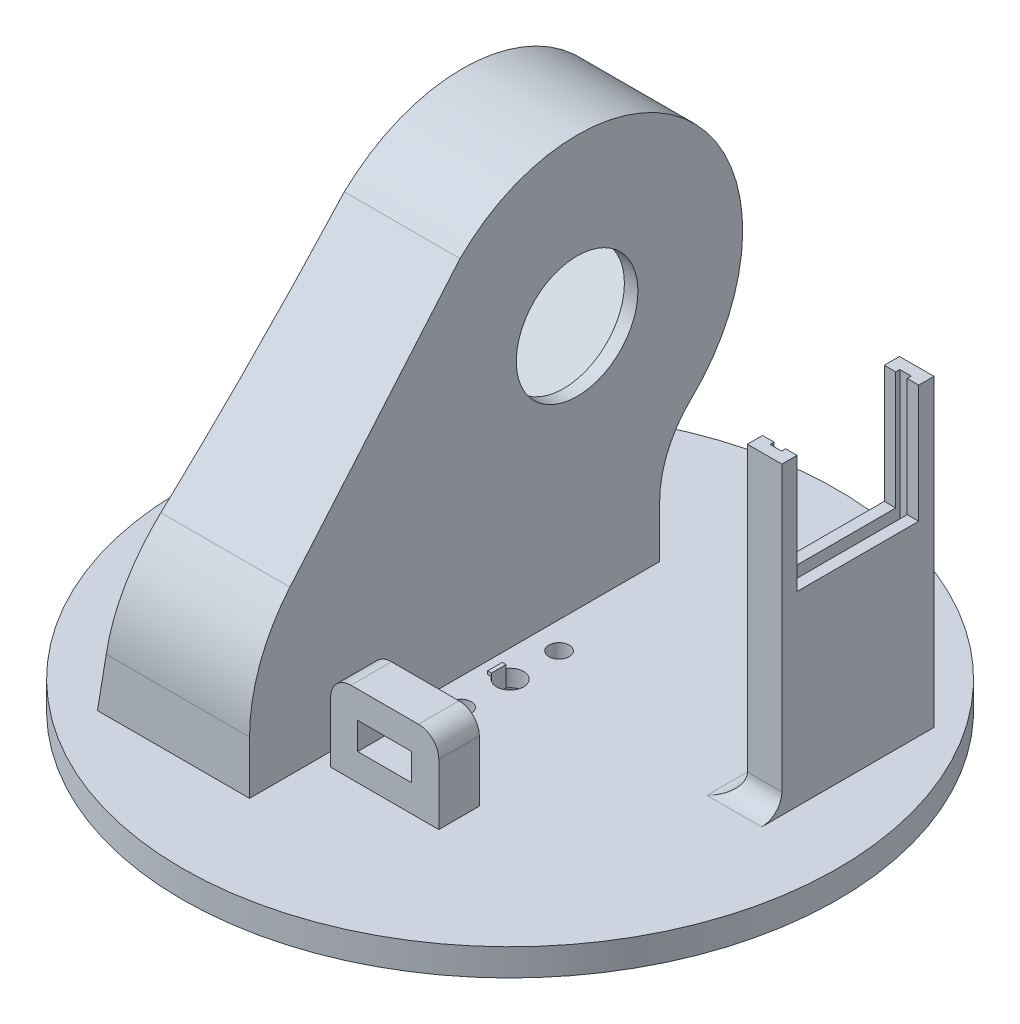
SolidWorks part; units mm, degrees
ref_plane "Front Plane" through (0, 0, 0) normal (0, 0, 1) x (1, 0, 0)
ref_plane "Top Plane" through (0, 0, 0) normal (0, 1, 0) x (1, 0, 0)
ref_plane "Right Plane" through (0, 0, 0) normal (1, 0, 0) x (0, 0, -1)
sketch "Sketch2" plane through (0, 0, 0) normal (0, 1, 0) x (1, 0, 0)
  circle A0 centre (0, 0) radius 48.5
  dimension "D1" = 97
extrude "Boss-Extrude1" add sketch "Sketch2" along normal blind 4
sketch "Sketch4" plane through (0, 0, 0) normal (0, -1, 0) x (1, 0, 0)
  circle A0 centre (0, 7.25) radius 1.5
  circle A1 centre (0, -7.25) radius 1.5
  dimension "D1" = 3
  dimension "D2" = 3
  dimension "D3" = 14.5
  dimension "D4" = 7.25
extrude "Cut-Extrude2" cut sketch "Sketch4" against normal through all
sketch "Sketch5" plane through (0, 0, 0) normal (0, -1, 0) x (1, 0, 0)
  circle A0 centre (0, 0) radius 3.75
  dimension "D1" = 7.5
extrude "Cut-Extrude3" cut sketch "Sketch5" against normal blind 1.5
ref_plane "Plane1" through (-4, 0, 0) normal (1, 0, 0) x (0, 0, -1)
sketch "Sketch7" plane through (-4, 0, 0) normal (1, 0, 0) x (0, 0, -1)
  line L0 (23.1299, 11.6445) -> (23.1299, 4)
  line L5 (48.5, 4) -> (-48.5, 4) construction
  line L6 (-27.2273, 29.5362) -> (-1.2843, 55.4793)
  line L7 (-43.5609, 4) -> (23.1299, 4)
  line L11 (-34.5496, 4) -> (-34.5496, 11.8586)
  arc A4 (28.7298, 24.692) -> (-1.2843, 55.4793) centre (13.9185, 40.2765) ccw
  arc A5 (28.7298, 24.692) -> (23.1299, 11.6445) centre (41.1299, 11.6445) ccw
  arc A6 (-27.2273, 29.5362) -> (-34.5496, 11.8586) centre (-9.5496, 11.8586) ccw
  dimension "D1" = 25
  dimension "D4" = 43
  dimension "D3" = 18
  dimension "D5" = 45
extrude "Boss-Extrude2" add sketch "Sketch7" against normal blind 14
ref_plane "Plane2" through (-6, 0, 0) normal (1, 0, 0) x (0, 0, -1)
sketch "Sketch8" plane through (-6, 0, 0) normal (1, 0, 0) x (0, 0, -1)
  line L0 (-27.2273, 29.5362) -> (-1.2843, 55.4793) construction
  line L1 (-15.2496, 25.9576) -> (13.7417, 54.9489)
  line L2 (-15.2496, 25.9576) -> (-0.4004, 11.1083)
  line L3 (-0.4004, 11.1083) -> (28.591, 40.0997)
  line L4 (13.7417, 54.9489) -> (28.591, 40.0997)
  line L5 (-15.2496, 25.9576) -> (28.591, 40.0997) construction
  line L6 (-0.4004, 11.1083) -> (13.7417, 54.9489) construction
  point P0 (6.6707, 33.0286)
  point P11 (13.9185, 40.2765)
  dimension "D1" = 41
  dimension "D2" = 21
  dimension "D3" = 90
  dimension "D4" = 20.5
  dimension "D5" = 90
  dimension "D6" = 10.25
  dimension "D7" = 10.5
extrude "Cut-Extrude5" cut sketch "Sketch8" against normal up to next
sketch "Sketch9" plane through (-18, 0, 0) normal (-1, 0, 0) x (0, 0, 1)
  line L0 (-13.7417, 54.9489) -> (-28.591, 40.0997) construction
  line L3 (-21.1664, 47.5243) -> (-22.536, 48.894) construction
  circle A0 centre (-20.1057, 53.5347) radius 1.3
  circle A1 centre (-27.1768, 46.4637) radius 1.3
  circle A2 centre (6.7644, 12.5225) radius 1.3
  circle A3 centre (13.8354, 19.5936) radius 1.3
  dimension "D1" = 2.6
  dimension "D5" = 5
  dimension "D6" = 90
  dimension "D2" = 3.5
  dimension "D3" = 2
  dimension "D4" = 2
extrude "Cut-Extrude6" cut sketch "Sketch9" against normal blind 7.5
sketch "Sketch11" plane through (-4, 0, 0) normal (1, 0, 0) x (0, 0, -1)
  circle A0 centre (13.9185, 40.2765) radius 9
  dimension "D1" = 18
extrude "Cut-Extrude9" cut sketch "Sketch11" against normal up to next
sketch "Sketch17" plane through (-18, 0, 0) normal (-1, 0, 0) x (0, 0, 1)
  line L0 (29.3486, 31.6576) -> (3.4056, 57.6006)
  line L1 (-26.1299, 11.6445) -> (-26.1299, 1)
  line L2 (-26.1299, 1) -> (37.5496, 1)
  line L3 (37.5496, 1) -> (37.5496, 11.8586)
  line L4 (27.2273, 29.5362) -> (1.2843, 55.4793)
  line L5 (-23.1299, 11.6445) -> (-23.1299, 4)
  line L6 (-23.1299, 4) -> (34.5496, 4)
  line L7 (34.5496, 4) -> (34.5496, 11.8586)
  line L9 (-23.1299, 11.6445) -> (-23.1299, 4)
  line L10 (-23.1299, 4) -> (34.5496, 4)
  line L11 (34.5496, 4) -> (34.5496, 11.8586)
  line L12 (-26.1299, 4) -> (37.5496, 4)
  line L13 (48.5, 4) -> (-48.5, 4) construction
  line L14 (3.4056, 57.6006) -> (28.5745, 28.0776)
  line L15 (1.2843, 55.4793) -> (26.295, 26.1272)
  line L16 (31.5496, 11.8586) -> (31.5496, 4)
  line L18 (27.2273, 29.5362) -> (1.2843, 55.4793) construction
  arc A0 (3.4056, 57.6006) -> (-30.7965, 22.5174) centre (-13.9185, 40.2765) ccw
  arc A1 (-26.1299, 11.6445) -> (-30.7965, 22.5174) centre (-41.1299, 11.6445) ccw
  arc A2 (37.5496, 11.8586) -> (29.3486, 31.6576) centre (9.5496, 11.8586) ccw
  arc A3 (1.2843, 55.4793) -> (-28.7298, 24.692) centre (-13.9185, 40.2765) ccw
  arc A4 (-23.1299, 11.6445) -> (-28.7298, 24.692) centre (-41.1299, 11.6445) ccw
  arc A5 (34.5496, 11.8586) -> (27.2273, 29.5362) centre (9.5496, 11.8586) ccw
  arc A6 (1.2843, 55.4793) -> (-28.7298, 24.692) centre (-13.9185, 40.2765) ccw
  arc A7 (-23.1299, 11.6445) -> (-28.7298, 24.692) centre (-41.1299, 11.6445) ccw
  arc A8 (34.5496, 11.8586) -> (27.2273, 29.5362) centre (9.5496, 11.8586) ccw
  arc A9 (31.5496, 11.8586) -> (25.106, 27.4149) centre (9.5496, 11.8586) ccw
  line M16 (27.2273, 29.5362) -> (1.2843, 55.4793)
  arc M17 (1.2843, 55.4793) -> (-28.7298, 24.692) centre (-13.9185, 40.2765) ccw
  arc M18 (-28.7298, 24.692) -> (-23.1299, 11.6445) centre (-41.1299, 11.6445) cw
  line M19 (-23.1299, 11.6445) -> (-23.1299, 4)
  line M21 (34.5496, 4) -> (34.5496, 11.8586)
  arc M22 (34.5496, 11.8586) -> (27.2273, 29.5362) centre (9.5496, 11.8586) ccw
  dimension "D1" = 0
  dimension "D2" = 3
  dimension "D3" = 3
extrude "Boss-Extrude7" add sketch "Sketch17" along normal blind 9 and the other way up to surface (14 mm away) contours A9 L16 L12 L15 M21 M22 M16 | A1 L1 L12 L14 A0 M19 M18 M17 M16 M22 other way up to face at (-4, 40.2765, -22.9185)
sketch "Sketch25" plane through (-18, 0, 0) normal (-1, 0, 0) x (0, 0, 1)
  line L0 (-23.1299, 11.6445) -> (-23.1299, 4)
  line L1 (48.5, 4) -> (-48.5, 4) construction
  line L2 (-23.1299, 11.6445) -> (-23.1299, 4) construction
  line L3 (1.2843, 55.4793) -> (26.295, 26.1272) construction
  line L4 (31.5496, 4) -> (-23.1299, 4) construction
  line L5 (31.5496, 11.8586) -> (31.5496, 4) construction
  line L6 (31.5496, 4) -> (-23.1299, 4)
  line L7 (31.5496, 11.8586) -> (31.5496, 4)
  line L8 (1.2843, 55.4793) -> (26.295, 26.1272)
  arc A0 (-23.1299, 11.6445) -> (-28.7298, 24.692) centre (-41.1299, 11.6445) ccw construction
  arc A1 (1.2843, 55.4793) -> (-28.7298, 24.692) centre (-13.9185, 40.2765) ccw construction
  arc A2 (-23.1299, 11.6445) -> (-28.7298, 24.692) centre (-41.1299, 11.6445) ccw
  arc A3 (31.5496, 11.8586) -> (26.295, 26.1272) centre (9.5496, 11.8586) ccw construction
  arc A4 (31.5496, 11.8586) -> (26.295, 26.1272) centre (9.5496, 11.8586) ccw
  spline S0 degree 3 poles (-28.7298, 24.692) (-21.9549, 18.2532) (-19.0941, 12.798) (-15.1299, 4) knots 0 0 0 0 1 1 1 1
  spline S1 degree 2 poles (11.7516, 43.195) (26.5513, 25.8264) (25.5496, 4) knots 0 0 0 1 1 1
  dimension "D2" = 8
  dimension "D1" = 6
extrude "Boss-Extrude10" add sketch "Sketch25" along normal up to surface (9 mm away) contours S0 L6 L0 A2 | A4 S1 A2 S0 L8 up to face at (-27, 22.2911, 0.3951)
sketch "Sketch26" plane through (0, 0, 0) normal (0, 0, 1) x (1, 0, 0)
  line L0 (-4, 64.7765) -> (-27, 64.7765) construction
  line L1 (-27, 4) -> (-4, 4) construction
  line L2 (-27, 4) -> (-27, 11.8586) construction
  line L3 (-26, 64.7765) -> (-27, 64.7765)
  line L4 (-27, 64.7765) -> (-27, 4)
  line L5 (-27, 4) -> (-23, 4)
  spline S0 degree 2 poles (-26, 64.7765) (-24.7724, 34.3751) (-23, 4) knots 0 0 0 1 1 1
  dimension "D1" = 1
  dimension "D2" = 4
  dimension "D3" = 2
extrude "Cut-Extrude15" [suppressed] cut sketch "Sketch26" against normal through all both and the other way through all contours L4 L5 S0 L3
sketch "Sketch27" plane through (0, 4, 0) normal (0, 1, 0) x (1, 0, 0)
  line L1 (-2, -18.5496) -> (14, -18.5496)
  line L2 (-2, -18.5496) -> (-2, -24.5496)
  line L3 (-2, -24.5496) -> (14, -24.5496)
  line L4 (14, -18.5496) -> (14, -24.5496)
  line L5 (-27, -34.5496) -> (-4, -34.5496) construction
  line L6 (-4, -34.5496) -> (-4, 26.1299) construction
  dimension "D1" = 10
  dimension "D2" = 6
  dimension "D3" = 16
  dimension "D4" = 2
extrude "Boss-Extrude11" add sketch "Sketch27" along normal blind 12
fillet "Fillet6" radius 3 2 edges at (14, 16, 21.5496) (-2, 16, 21.5496)
sketch "Sketch28" plane through (0, 0, 24.5496) normal (0, 0, 1) x (1, 0, 0)
  line L8 (10, 12) -> (2, 12)
  line L9 (2, 12) -> (2, 8)
  line L10 (2, 8) -> (10, 8)
  line L11 (10, 8) -> (10, 12)
  line L12 (10, 12) -> (2, 12)
  line L13 (2, 12) -> (2, 8)
  line L14 (2, 8) -> (10, 8)
  line L15 (10, 8) -> (10, 12)
  dimension "D1" = 4
extrude "Cut-Extrude16" cut sketch "Sketch28" against normal up to next
sketch "Sketch29" plane through (0, 0, 0) normal (0, 0, 1) x (1, 0, 0)
  line L0 (-4, 64.7765) -> (-27, 64.7765) construction
  line L1 (-27, 4) -> (-4, 4) construction
  line L2 (-21, 64.7765) -> (-27, 64.7765)
  line L3 (-27, 64.7765) -> (-27, 4)
  line L4 (-27, 4) -> (-26.5, 4)
  line L5 (48.5, 4) -> (-48.5, 4) construction
  spline S0 degree 2 poles (-21, 64.7765) (-21.2205, 34.1409) (-26.5, 4) knots 0 0 0 1 1 1
  dimension "D1" = 6
  dimension "D2" = 4
  dimension "D3" = 0.5
  dimension "D4" = 25
extrude "Cut-Extrude17" cut sketch "Sketch29" against normal through all both and the other way through all
sketch "Croquis4" plane through (0, 4, 0) normal (0, 1, 0) x (1, 0, 0)
  line L1 (32.45, 2.6699) -> (37.55, 2.6699)
  line L2 (32.45, 2.6699) -> (32.45, 25.1699)
  line L3 (32.45, 25.1699) -> (37.55, 25.1699)
  line L4 (37.55, 2.6699) -> (37.55, 25.1699)
  line L5 (32.45, 2.6699) -> (37.55, 25.1699) construction
  line L6 (32.45, 25.1699) -> (37.55, 2.6699) construction
  line L8 (-4, 26.1299) -> (-26.5, 26.1299) construction
  line L9 (-4, -34.5496) -> (-4, 26.1299) construction
  point P0 (35, 13.9199)
  dimension "D1" = 12.21
  dimension "D2" = 39
  dimension "D3" = 5.1
  dimension "D4" = 22.5
extrude "Saliente-Extruir1" add sketch "Croquis4" along normal blind 45
sketch "Croquis5" plane through (0, 49, 0) normal (0, 1, 0) x (1, 0, 0)
  line L0 (37.55, 2.6699) -> (37.55, 25.1699) construction
  line L1 (34.15, 4.3199) -> (35.85, 4.3199)
  line L2 (34.15, 4.3199) -> (34.15, 23.5199)
  line L3 (34.15, 23.5199) -> (35.85, 23.5199)
  line L4 (35.85, 4.3199) -> (35.85, 23.5199)
  line L5 (34.15, 4.3199) -> (35.85, 23.5199) construction
  line L6 (34.15, 23.5199) -> (35.85, 4.3199) construction
  line L7 (37.55, 25.1699) -> (32.45, 25.1699) construction
  point P0 (35, 13.9199)
  dimension "D1" = 1.7
  dimension "D2" = 2.55
  dimension "D3" = 11.25
  dimension "D4" = 19.2
extrude "Cortar-Extruir1" cut sketch "Croquis5" against normal blind 19.5
sketch "Croquis6" plane through (37.55, 0, 0) normal (1, 0, 0) x (0, 0, -1)
  line L0 (2.6699, 49) -> (25.1699, 49) construction
  line L1 (4.9185, 31.553) -> (22.9185, 31.553)
  line L2 (4.9185, 31.553) -> (4.9185, 49)
  line L3 (4.9185, 49) -> (22.9185, 49)
  line L4 (22.9185, 31.553) -> (22.9185, 49)
  line L5 (4.9185, 31.553) -> (22.9185, 49) construction
  line L6 (4.9185, 49) -> (22.9185, 31.553) construction
  point P0 (13.9185, 40.2765)
extrude "Cortar-Extruir2" cut sketch "Croquis6" against normal blind 19.5
fillet "Redondeo1" radius 3 2 edges at (35, 4, -2.6699) (32.45, 4, -13.9199)
sketch "Croquis7" plane through (0, 1.5, 0) normal (0, -1, 0) x (1, 0, 0)
  line L0 (-1.67, -1.0822) -> (-1.67, 1.0822)
  line L1 (-1.67, -1.0822) -> (-1.67, 1.0822)
  circle A0 centre (0, 0) radius 1.99
  dimension "D1" = 3.98
  dimension "D2" = 1.67
extrude "Cortar-Extruir3" cut sketch "Croquis7" against normal blind 10 contours A0
sketch "Croquis8" plane through (0, 1.5, 0) normal (0, -1, 0) x (1, 0, 0)
  line L0 (-1.67, 1.0822) -> (-1.67, -1.0822)
  line L1 (-1.67, 1.0822) -> (-2.2341, 1.0822)
  line L2 (-2.2341, 1.0822) -> (-2.2341, -1.0822)
  line L3 (-2.2341, -1.0822) -> (-1.67, -1.0822)
  circle A0 centre (0, 0) radius 1.99 construction
  dimension "D1" = 1.67
extrude "Saliente-Extruir2" add sketch "Croquis8" against normal blind 3
